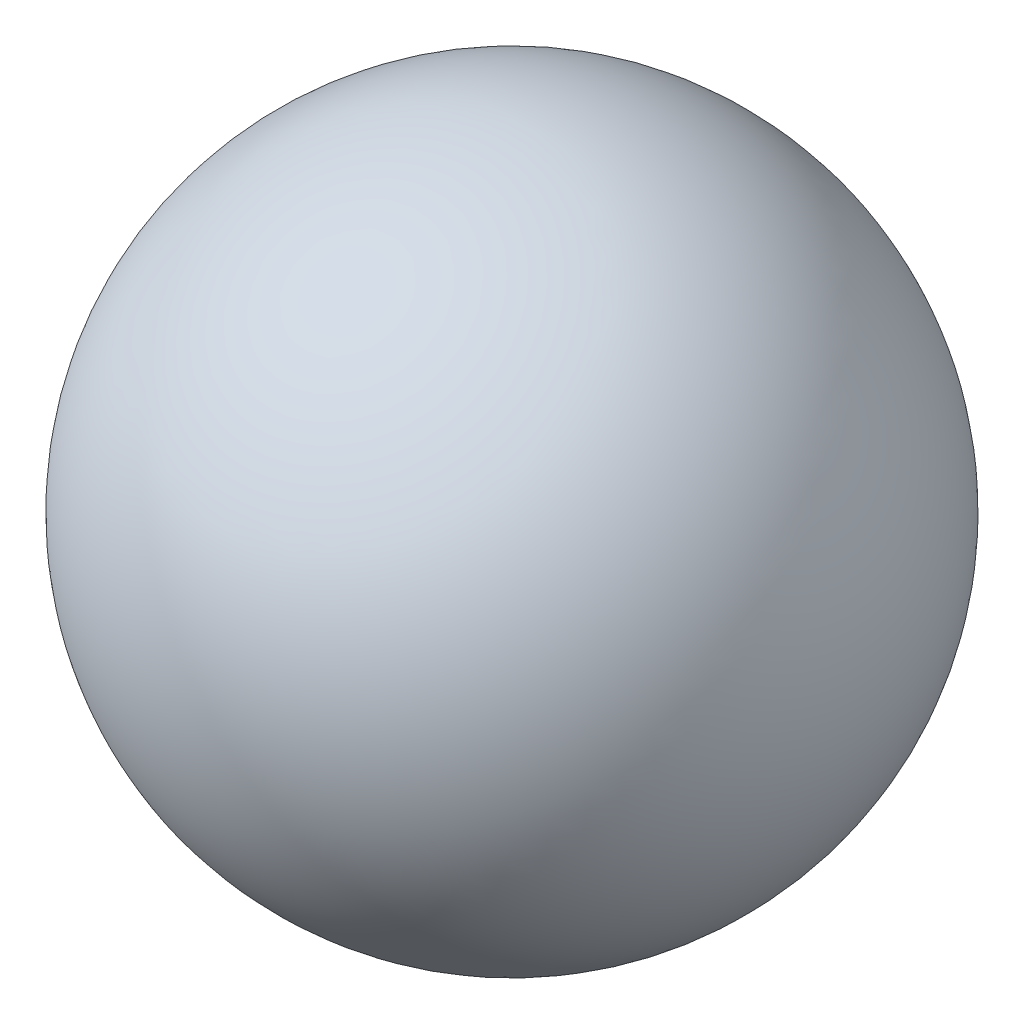
SolidWorks part; units mm, degrees
material "TIMETAL 35A CP Titanium (ASTM Grade 1) 99.1 Ti"
ref_plane "Front Plane" through (0, 0, 0) normal (0, 0, 1) x (1, 0, 0)
ref_plane "Top Plane" through (0, 0, 0) normal (0, 1, 0) x (1, 0, 0)
ref_plane "Right Plane" through (0, 0, 0) normal (1, 0, 0) x (0, 0, -1)
sketch "Sketch2" plane through (0, 0, 0) normal (0, 1, 0) x (1, 0, 0)
  line L0 (0, 183.8) -> (0, -183.8)
  arc A4 (0, 183.8) -> (0, -183.8) centre (0, 0) cw
  dimension "D1" = 367.6
revolve "Revolve1" add sketch "Sketch2" angle 360 about L0
